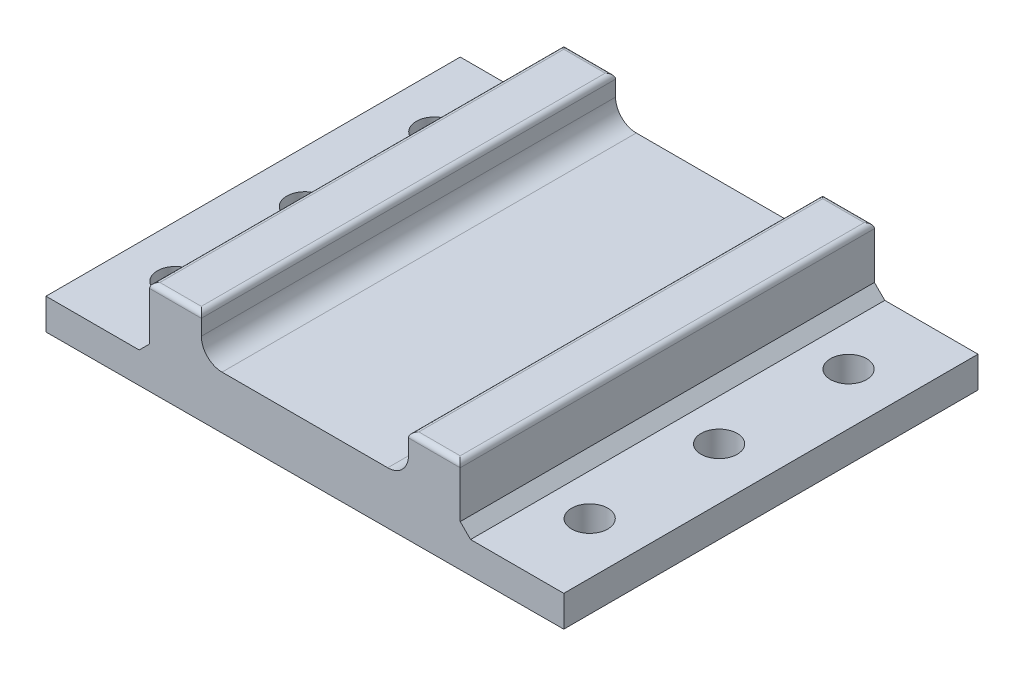
SolidWorks part; units mm, degrees
ref_plane "Plan de face" through (0, 0, 0) normal (0, 0, 1) x (1, 0, 0)
ref_plane "Plan de dessus" through (0, 0, 0) normal (0, 1, 0) x (1, 0, 0)
ref_plane "Plan de droite" through (0, 0, 0) normal (1, 0, 0) x (0, 0, -1)
sketch "Esquisse16" plane through (0, 0, 0) normal (0, 0, 1) x (1, 0, 0)
  line L0 (0, 0) -> (10, 0)
  line L1 (10, 0) -> (10, -8)
  line L2 (10, -8) -> (50, -8)
  line L3 (50, -8) -> (50, 0)
  line L4 (50, 0) -> (60, 0)
  line L5 (60, 0) -> (60, -12)
  line L6 (60, -12) -> (80, -12)
  line L7 (80, -12) -> (80, -18)
  line L8 (80, -18) -> (-20, -18.2989)
  line L9 (-20, -18.2989) -> (-20, -12.2989)
  line L10 (-20, -12.2989) -> (0, -12.2989)
  line L11 (0, -12.2989) -> (0, 0)
  dimension "D1" = 100
  dimension "D2" = 20
  dimension "D3" = 20
  dimension "D4" = 40
  dimension "D5" = 6
  dimension "D6" = 6
  dimension "D7" = 10
  dimension "D8" = 8
  dimension "D9" = 12
extrude "Boss.-Extru.3" add sketch "Esquisse16" against normal blind 80
sketch "Esquisse17" plane through (0, -12.2989, 0) normal (0, 1, 0) x (1, 0, 0)
  line L0 (-10, 80) -> (-10, 0) construction
  line L1 (0, 80) -> (-20, 80) construction
  line L2 (0, 0) -> (-20, 0) construction
  circle A0 centre (-10, 65) radius 3.5
  circle A1 centre (-10, 40) radius 3.5
  circle A2 centre (-10, 15) radius 3.5
  dimension "D1" = 7
  dimension "D2" = 7
  dimension "D3" = 7
  dimension "D4" = 15
  dimension "D5" = 15
extrude "Enlèv. mat.-Extru.4" cut sketch "Esquisse17" against normal through all
sketch "Esquisse18" plane through (0, -12, 0) normal (0, 1, 0) x (1, 0, 0)
  line L0 (70, 80) -> (70, 0) construction
  line L1 (80, 80) -> (60, 80) construction
  line L2 (80, 0) -> (60, 0) construction
  circle A0 centre (70, 65) radius 3.5
  circle A1 centre (70, 40) radius 3.5
  circle A2 centre (70, 15) radius 3.5
  dimension "D1" = 7
  dimension "D2" = 7
  dimension "D3" = 7
  dimension "D4" = 15
  dimension "D5" = 15
extrude "Enlèv. mat.-Extru.5" cut sketch "Esquisse18" against normal through all
chamfer "Chanfrein5" distance 2 angle 45 2 edges at (0, -12.2989, -40) (60, -12, -40)
fillet "Congé1" radius 4 2 edges at (50, -8, -40) (10, -8, -40)
fillet "Congé2" radius 1 8 edges at (0, 0, -40) (5, 0, -80) (10, 0, -40) (5, 0, 0) (50, 0, -40) (55, 0, -80) (60, 0, -40) (55, 0, 0)
